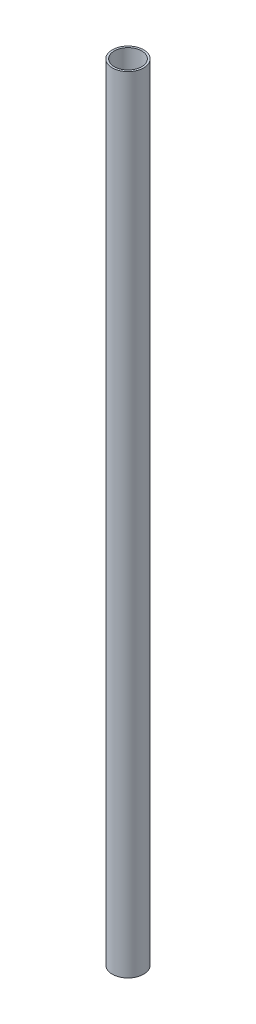
SolidWorks part; units mm, degrees
ref_plane "Front Plane" through (0, 0, 0) normal (0, 0, 1) x (1, 0, 0)
ref_plane "Top Plane" through (0, 0, 0) normal (0, 1, 0) x (1, 0, 0)
ref_plane "Right Plane" through (0, 0, 0) normal (1, 0, 0) x (0, 0, -1)
sketch "Sketch1" plane through (0, 0, 0) normal (0, 1, 0) x (1, 0, 0)
  circle A0 centre (0, 0) radius 4
  circle A1 centre (0, 0) radius 3.5
  dimension "D1" = 8
  dimension "D2" = 7
extrude "Boss-Extrude1" add sketch "Sketch1" along normal blind 200
